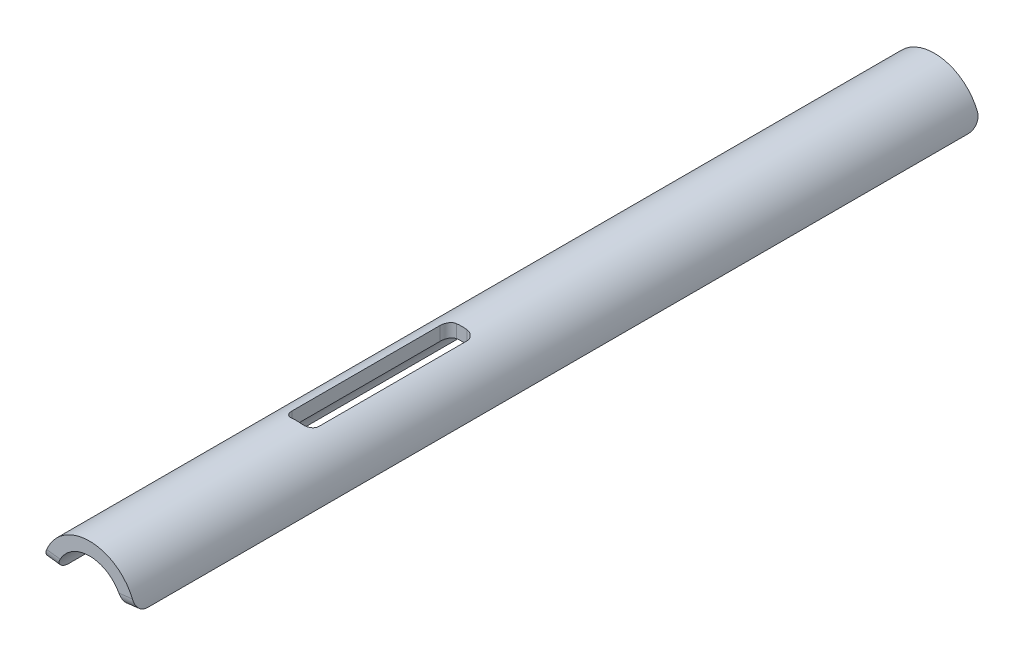
SolidWorks part; units mm, degrees
material "A-Glass Fiber"
ref_plane "Front Plane" through (0, 0, 0) normal (0, 0, 1) x (1, 0, 0)
ref_plane "Top Plane" through (0, 0, 0) normal (0, 1, 0) x (1, 0, 0)
ref_plane "Right Plane" through (0, 0, 0) normal (1, 0, 0) x (0, 0, -1)
sketch "Sketch1" plane through (0, 0, 0) normal (0, 0, 1) x (1, 0, 0)
  line L0 (40.7544, 5) -> (11.0867, 5) construction
  line L1 (40.7544, 5) -> (56.5113, 6.9331)
  line L2 (0, 0) -> (0, -11.7162) construction
  line L3 (-40.7544, 5) -> (-56.5113, 6.9331)
  arc A0 (40.7544, 5) -> (-40.7544, 5) centre (0, 0) ccw
  arc A1 (56.5113, 6.9331) -> (-56.5113, 6.9331) centre (0, 0) ccw
  dimension "D1" = 82.12
  dimension "D2" = 113.87
  dimension "D3" = 5
extrude "Boss-Extrude1" add sketch "Sketch1" along normal mid plane 1039
fillet "Fillet1" radius 15 4 edges at (-48.6329, 5.9666, -519.5) (48.6329, 5.9666, -519.5) (-48.6329, 5.9666, 519.5) (48.6329, 5.9666, 519.5)
ref_plane "Plane4" through (0, 0, 67) normal (0, 0, 1) x (1, 0, 0)
sketch "Sketch2" plane through (0, 0, 0) normal (0, 1, 0) x (1, 0, 0)
  line L0 (0, 0) -> (0, -107.6084) construction
  line L1 (16.5, -264) -> (-16.5, -264)
  line L2 (16.5, -264) -> (16.5, -62)
  line L3 (16.5, -62) -> (-16.5, -62)
  line L4 (-16.5, -264) -> (-16.5, -62)
  line L5 (16.5, -264) -> (-16.5, -62) construction
  line L6 (16.5, -62) -> (-16.5, -264) construction
  line L7 (0, 0) -> (133.0686, 0) construction
  point P0 (0, -163)
  dimension "D1" = 62
  dimension "D2" = 33
  dimension "D3" = 264
extrude "Cut-Extrude1" cut sketch "Sketch2" along normal through all
fillet "Fillet2" radius 10 4 edges at (-16.5, 46.0453, 62) (16.5, 46.0453, 62) (-16.5, 46.0453, 264) (16.5, 46.0453, 264)
